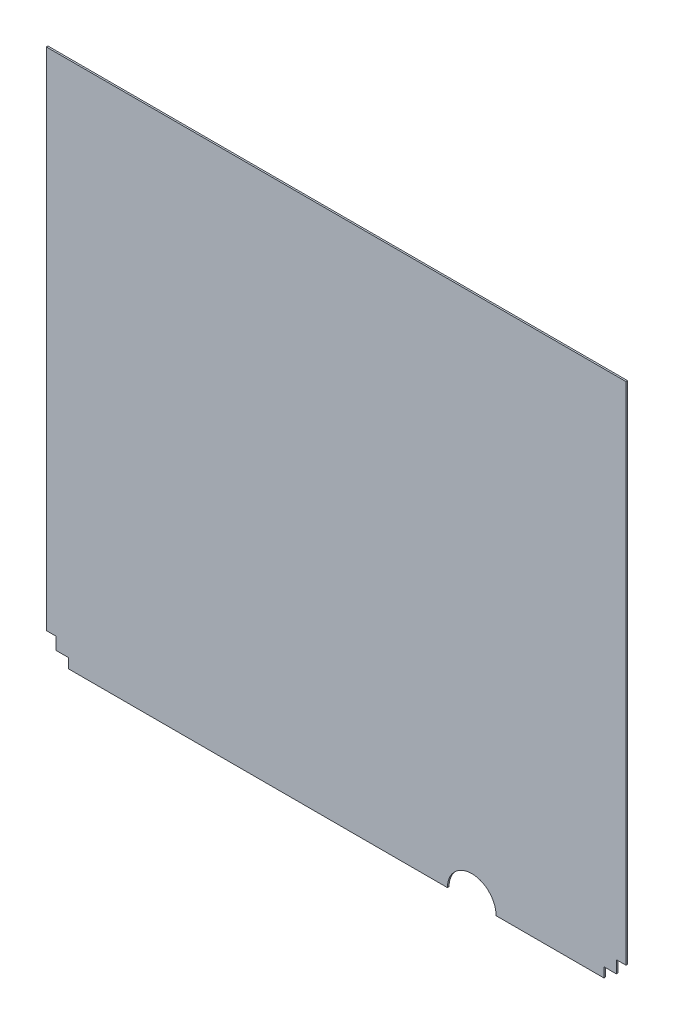
SolidWorks part; units mm, degrees
ref_plane "Front Plane" through (0, 0, 0) normal (0, 0, 1) x (1, 0, 0)
ref_plane "Top Plane" through (0, 0, 0) normal (0, 1, 0) x (1, 0, 0)
ref_plane "Right Plane" through (0, 0, 0) normal (1, 0, 0) x (0, 0, -1)
sketch "Sketch1" plane through (0, 0, 0) normal (0, 0, 1) x (1, 0, 0)
  line L0 (0, 34.544) -> (15.24, 34.544)
  line L1 (0, 0) -> (907.001, 0)
  line L2 (0, 0) -> (0, 825.5)
  line L3 (0, 825.5) -> (907.001, 825.5)
  line L4 (907.001, 0) -> (907.001, 825.5)
  line L5 (0, 0) -> (914.4, 0) construction
  line L6 (0, 0) -> (0, 914.4) construction
  line L7 (0, 914.4) -> (914.4, 914.4) construction
  line L8 (914.4, 0) -> (914.4, 914.4) construction
  line L9 (15.24, 34.544) -> (15.24, 15.24)
  line L10 (15.24, 15.24) -> (34.544, 15.24)
  line L11 (34.544, 15.24) -> (34.544, 0)
  line L12 (907.001, 34.544) -> (891.761, 34.544)
  line L13 (891.761, 34.544) -> (891.761, 15.24)
  line L14 (891.761, 15.24) -> (872.457, 15.24)
  line L15 (872.457, 15.24) -> (872.457, 0)
  arc A0 (703.801, 0) -> (627.601, 0) centre (665.701, 0) ccw
  dimension "D13" = 38.1
  dimension "D1" = 825.5
  dimension "D2" = 907.001
  dimension "D3" = 914.4
  dimension "D4" = 914.4
  dimension "D5" = 15.24
  dimension "D6" = 15.24
  dimension "D7" = 34.544
  dimension "D8" = 34.544
  dimension "D9" = 15.24
  dimension "D10" = 15.24
  dimension "D11" = 34.544
  dimension "D12" = 34.544
  dimension "D14" = 203.2
extrude "Boss-Extrude1" add sketch "Sketch1" along normal blind 2.54 contours L15 L14 L13 L12 L4 L3 L2 L0 L9 L10 L11 L1
